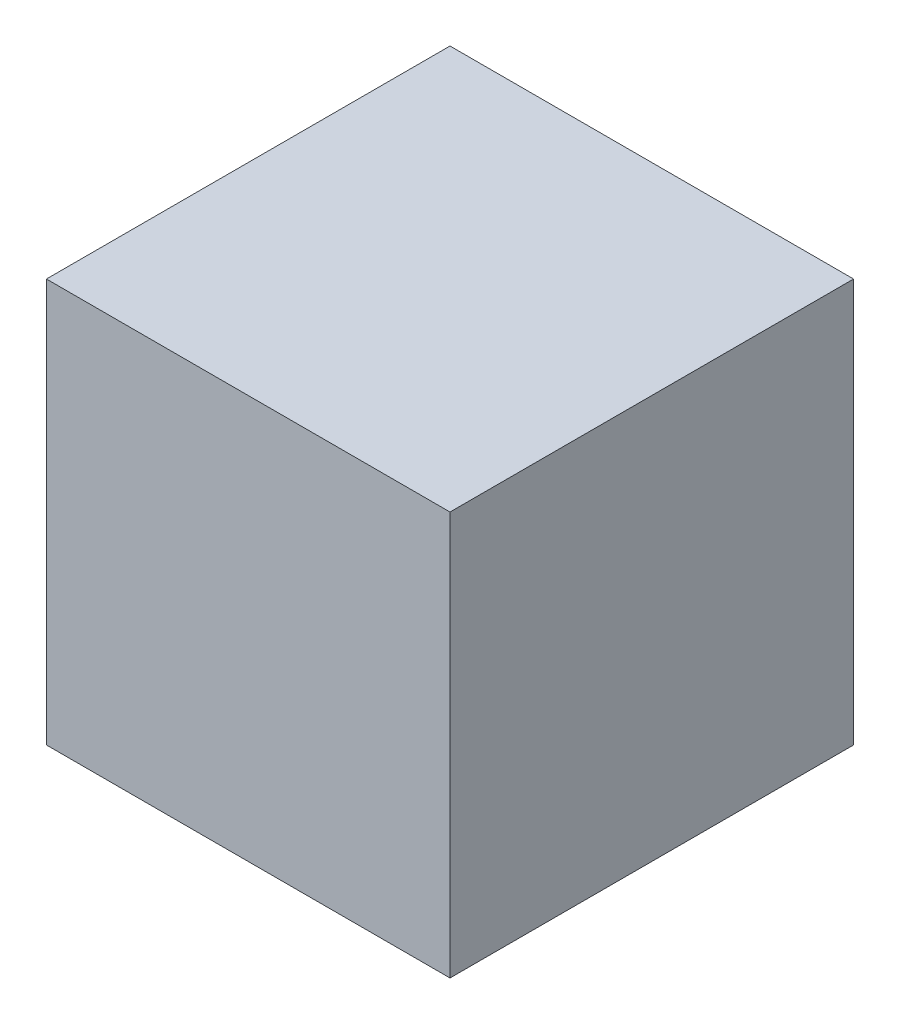
SolidWorks part; units mm, degrees
ref_plane "Alzado" through (0, 0, 0) normal (0, 0, 1) x (1, 0, 0)
ref_plane "Planta" through (0, 0, 0) normal (0, 1, 0) x (1, 0, 0)
ref_plane "Vista lateral" through (0, 0, 0) normal (1, 0, 0) x (0, 0, -1)
sketch "Croquis1" plane through (0, 0, 0) normal (0, 0, 1) x (1, 0, 0)
  line L1 (-30, 30) -> (30, 30)
  line L2 (-30, 30) -> (-30, -30)
  line L3 (-30, -30) -> (30, -30)
  line L4 (30, 30) -> (30, -30)
  line L5 (-30, 30) -> (30, -30) construction
  line L6 (-30, -30) -> (30, 30) construction
  point P0 (0, 0)
  dimension "D1" = 60
  dimension "D2" = 60
extrude "Saliente-Extruir1" add sketch "Croquis1" along normal blind 60
